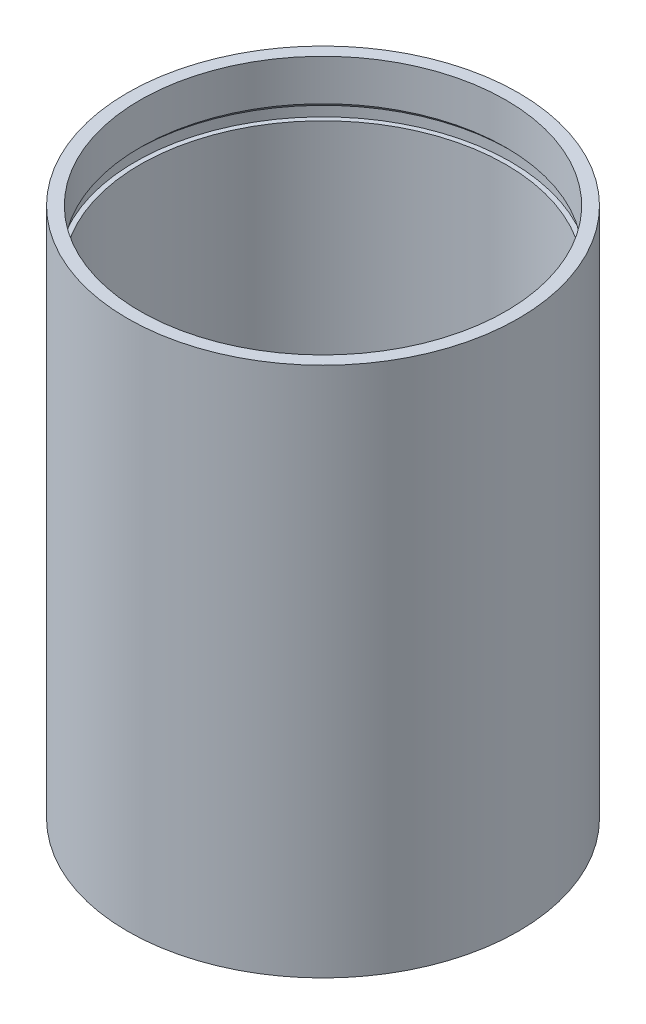
SolidWorks part; units mm, degrees
material "1.4404 (X2CrNiMo17-12-2)"
ref_plane "Ebene vorne" through (0, 0, 0) normal (0, 0, 1) x (1, 0, 0)
ref_plane "Ebene oben" through (0, 0, 0) normal (0, 1, 0) x (1, 0, 0)
ref_plane "Ebene rechts" through (0, 0, 0) normal (1, 0, 0) x (0, 0, -1)
sketch "Sketch1" plane through (0, 0, 0) normal (0, 0, 1) x (1, 0, 0)
  line L0 (0, 0) -> (0, 67.5051) construction
  line L1 (0, 0) -> (-45.3246, 0) construction
  line L2 (-45.85, -52.5) -> (-45.85, 52.5)
  line L3 (-45.85, 52.5) -> (-47.05, 52.5)
  line L4 (-47.05, 52.5) -> (-47.05, 55)
  line L5 (-47.05, 55) -> (-45.85, 56.2)
  line L6 (-45.85, 56.2) -> (-45.85, 66.5)
  line L8 (-45.85, 66.5) -> (-49, 66.5)
  line L9 (-49, 66.5) -> (-49, -66.5)
  line L10 (-45.85, -66.5) -> (-49, -66.5)
  line L12 (-45.85, -56.2) -> (-45.85, -66.5)
  line L13 (-47.05, -55) -> (-45.85, -56.2)
  line L14 (-47.05, -52.5) -> (-47.05, -55)
  line L15 (-45.85, -52.5) -> (-47.05, -52.5)
  point P14 (-49, 0)
  point P20 (-45.85, 0)
  dimension "D1" = 49
  dimension "D2" = 45.85
  dimension "D3" = 1.2
  dimension "D4" = 45
  dimension "D5" = 14
  dimension "D6" = 2.5
  dimension "D7" = 55
revolve "Revolve1" add sketch "Sketch1" angle 360 about L0
ref_plane "Plane1" through (49, 0, 0) normal (1, 0, 0) x (0, 0, -1)
sketch "Sketch3" plane through (49, 0, 0) normal (1, 0, 0) x (0, 0, -1)
  line L1 (45.85, 66.5) -> (-45.85, 66.5) construction
  circle A0 centre (0, 46.5) radius 1.6
  dimension "D1" = 3.2
  dimension "D2" = 20
